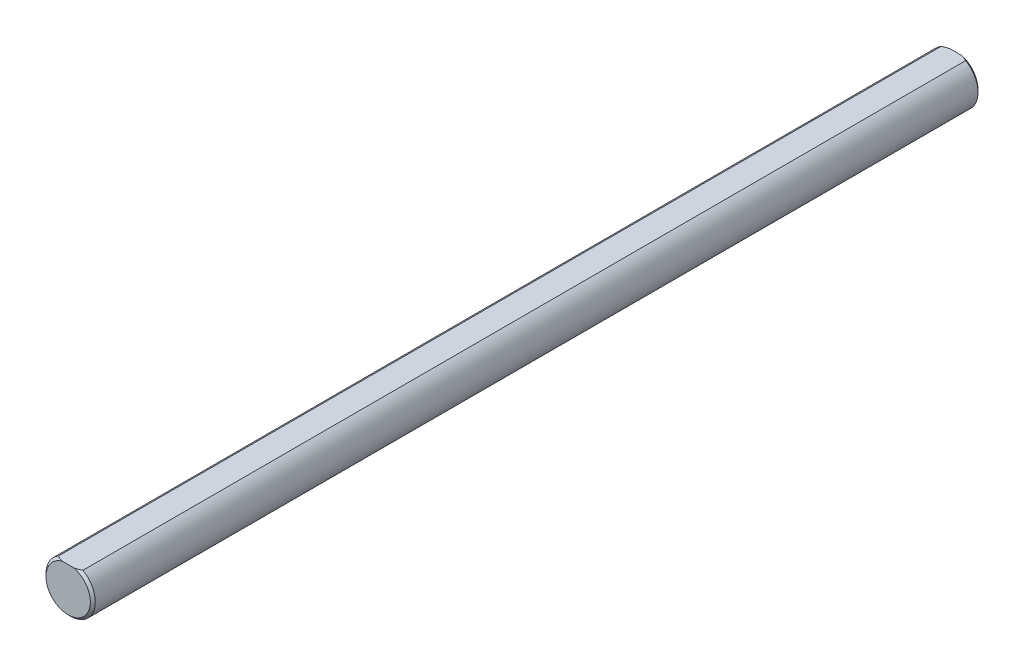
SolidWorks part; units mm, degrees
ref_plane "Front Plane" through (0, 0, 0) normal (0, 0, 1) x (1, 0, 0)
ref_plane "Top Plane" through (0, 0, 0) normal (0, 1, 0) x (1, 0, 0)
ref_plane "Right Plane" through (0, 0, 0) normal (1, 0, 0) x (0, 0, -1)
sketch "Sketch1" plane through (0, 0, 0) normal (0, 0, 1) x (1, 0, 0)
  line L0 (-1.5875, 2.7496) -> (1.5875, 2.7496) construction
  circle A1 centre (0, 0) radius 3.175 construction
  dimension "Diameter" = 6.35
  dimension "Flat Width" = 3.175
sketch "Sketch2" plane through (0, 0, 0) normal (1, 0, 0) x (0, 0, -1)
  line L0 (-57.15, 3.175) -> (57.15, 3.175) construction
  line L1 (0, 3.175) -> (0, -3.175) construction
  line L2 (0, 3.175) -> (0, -3.175) construction
  line L3 (-57.15, 3.175) -> (-57.15, -3.175) construction
  line L4 (-57.15, -3.175) -> (57.15, -3.175) construction
  point P2 (0, 3.175)
  point P3 (44.45, 3.175)
  point P4 (-44.45, 3.175)
  point P10 (76.0922, 3.175)
  point P13 (0, 0)
  dimension "D2" = 12.7
  dimension "D1" = 12.7
  dimension "D-Profile Length" = 114.3
  dimension "D3" = 114.3
sketch "Sketch3" plane through (0, 0, 0) normal (0, 0, 1) x (1, 0, 0)
  circle A1 centre (0, 0) radius 3.175 construction
  circle A3 centre (0, 0) radius 3.175
extrude "Boss-Extrude2" add sketch "Sketch3" along normal up to vertex (57.15 mm away) and the other way up to vertex (57.15 mm away) up to point (0, 3.175, 57.15) other way up to point (0, 3.175, -57.15)
sketch "Sketch10" plane through (0, 0, 0) normal (0, 0, 1) x (1, 0, 0)
  line L0 (-1.5875, 2.7496) -> (1.5875, 2.7496)
  line L1 (0, 0) -> (0, 3.175) construction
  circle A0 centre (0, 0) radius 3.175 construction
  circle A1 centre (0, 0) radius 3.175 construction
  arc A2 (-1.5875, 2.7496) -> (1.5875, 2.7496) centre (0, 0) cw
extrude "Cut-Extrude5" cut sketch "Sketch10" against normal through all both and the other way through all
chamfer "Chamfer1" distance 0.3175 angle 45 4 edges at (0, -3.175, 57.15) (0, -3.175, -57.15) (0, 2.7496, -57.15) (0, 2.7496, 57.15)
equation "\"D1@Chamfer1\"= \"Diameter@Sketch1\" / 20"
equation "\"D1@Sketch2\"=\"Diameter@Sketch1\"*2"
equation "\"D2@Sketch2\"=\"D1@Sketch2\""
